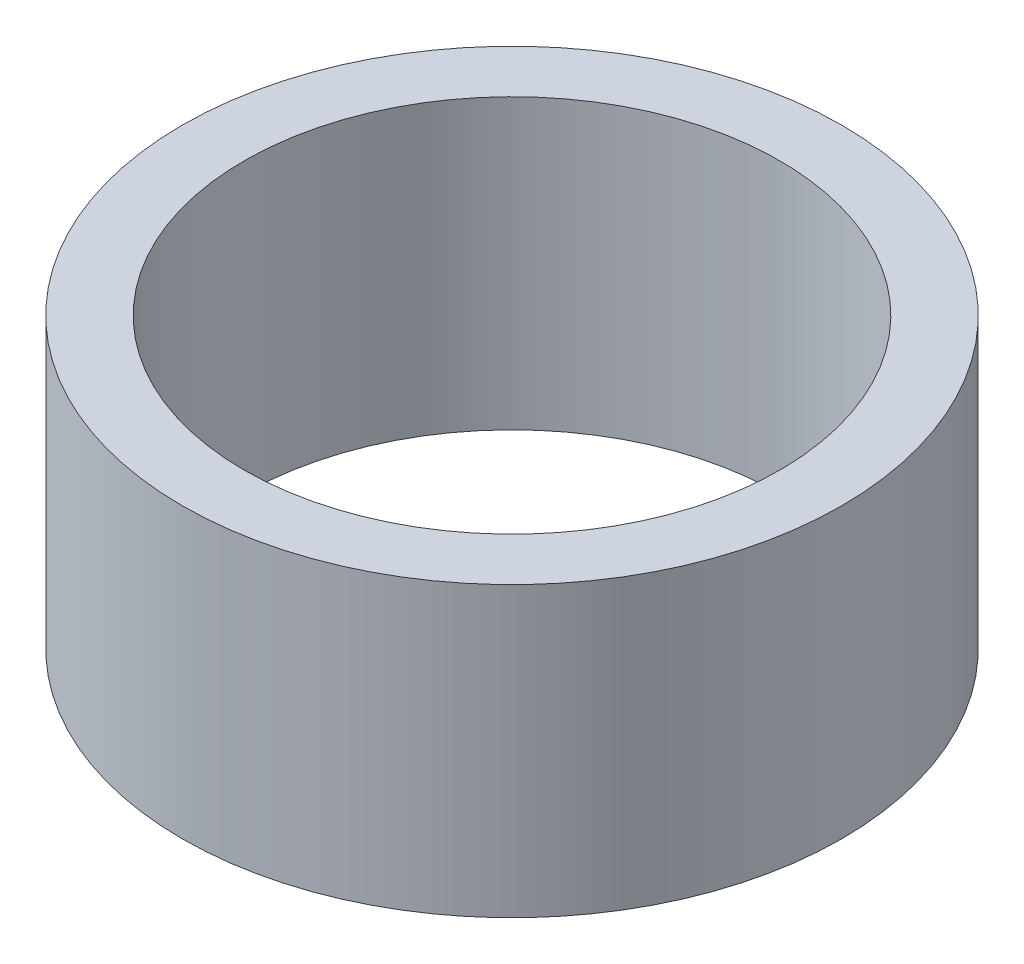
SolidWorks part; units mm, degrees
ref_plane "Front Plane" through (0, 0, 0) normal (0, 0, 1) x (1, 0, 0)
ref_plane "Top Plane" through (0, 0, 0) normal (0, 1, 0) x (1, 0, 0)
ref_plane "Right Plane" through (0, 0, 0) normal (1, 0, 0) x (0, 0, -1)
sketch "Sketch1" plane through (0, 0, 0) normal (0, 1, 0) x (1, 0, 0)
  circle A0 centre (0, 0) radius 13
  dimension "D1" = 26
extrude "Extrude-Thin1" add sketch "Sketch1" along normal blind 14 thin
